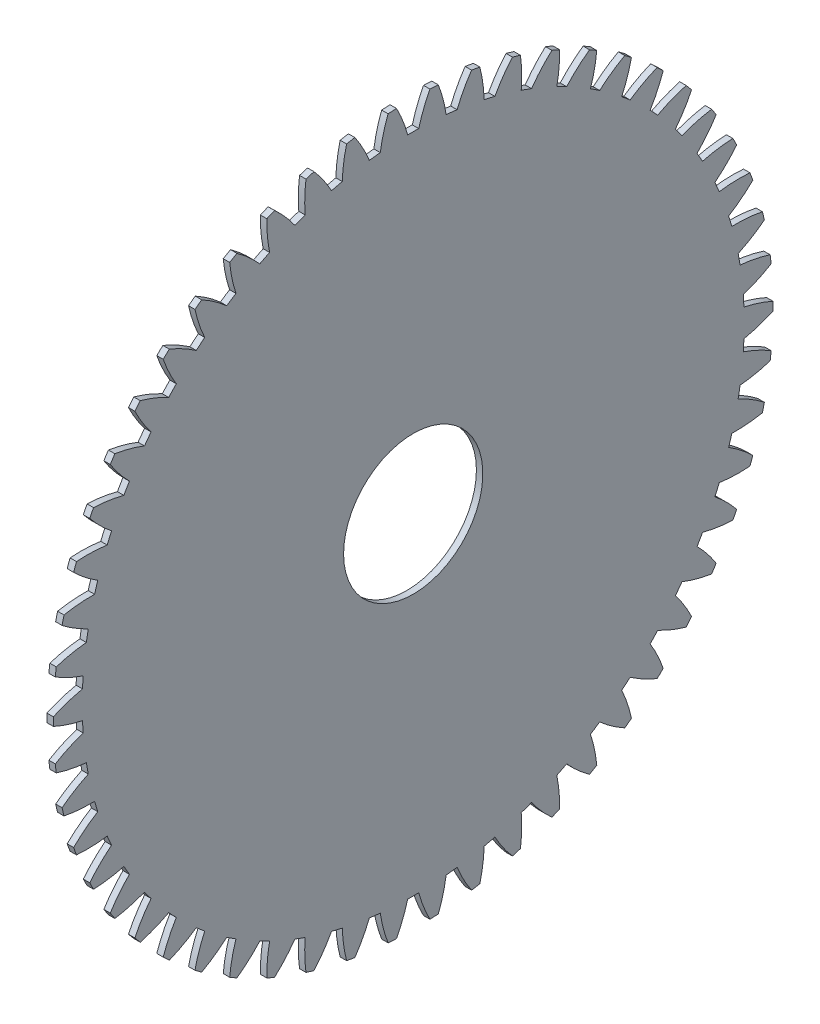
SolidWorks part; units mm, degrees
ref_plane "Plane1" through (0, 0, 0) normal (0, 0, 1) x (1, 0, 0)
ref_plane "Plane2" through (0, 0, 0) normal (0, 1, 0) x (1, 0, 0)
ref_plane "Plane3" through (0, 0, 0) normal (1, 0, 0) x (0, 0, -1)
other "Configuration Table"
sketch "HoldingSke" plane through (0, 0, 0) normal (0, 1, 0) x (1, 0, 0)
  line L0 (0, 0) -> (0.098, -0.1348)
  line L1 (-15, 0) -> (100, 0) construction
  line L2 (0, 0) -> (-2.1039, 2.3779)
  line L3 (0, 0) -> (-11.863, 4.5341)
  line L4 (0, 0) -> (5.0761, 6.9867)
  line L5 (0, 0) -> (-46.8476, -17.4728)
  line L6 (0, 0) -> (-2.4869, -1.6779)
  line L7 (-2.1039, 2.3779) -> (8.6586, 51.2059)
  line L8 (-76.2, 54.61) -> (-71.3, 54.61)
  line L9 (-71.009, 38.7566) -> (-53.1078, 45.2721)
  line L10 (-76.2, 71.12) -> (104.1128, 71.12)
  line L11 (0, 0) -> (-3, 0)
  line L12 (-76.2, 101.6) -> (-75.993, 101.6)
  line L13 (24.9733, 27.94) -> (52.9518, 28.4284)
  line L14 (24.9733, 27.94) -> (24.9743, 27.94)
  line L15 (24.9733, 27.94) -> (100.4006, 29.5858)
  line L16 (-63.627, -6) -> (-12.827, -6)
  circle A0 centre (0, 0) radius 32.5
  circle A1 centre (0, 0) radius 37.5
  circle A2 centre (0, 0) radius 37.5
  circle A3 centre (0, 0) radius 32.5
  dimension "MHD" = 75
  dimension "Hub_dia" = 75
  dimension "Bore" = 65
  dimension "MBD" = 65
  dimension "Num_teeth" = 54
  dimension "Pitch" = 0.1667
  dimension "Overall_len" = 50
  dimension "Show_teeth" = 54
  dimension "Thickness" = 3
  dimension "OAL" = 50.0001
  dimension "T_dim" = 4.9
  dimension "Ap" = 20
  dimension "H" = 19.05
  dimension "Pitch_radius" = 180.3128
  dimension "Width" = 3
  dimension "Backlash" = 0.207
  dimension "Addendum_fac" = 1
  dimension "Dedendum_fac" = 1.25
  dimension "Clearance_fac" = 0.25
  dimension "Dedendum_add" = 0.001
  dimension "Module" = 6
sketch "BasProSke" plane through (0, 0, 0) normal (0, 1, 0) x (1, 0, 0)
  line L0 (-10, 0) -> (60, 0) construction
  line L1 (0, 0) -> (0, 168)
  line L2 (0, 0) -> (3, 0)
  line L3 (3, 0) -> (3, 168)
  line L4 (3, 168) -> (0, 168)
  dimension "Thickness" = 3
  dimension "Diameter" = 336
revolve "Base-Revolve" add sketch "BasProSke" angle 360 about L0
sketch "TooCutSke" plane through (0, 0, 0) normal (1, 0, 0) x (0, 0, -1)
  line L1 (0, 0) -> (0, 107) construction
  line L2 (0, 0) -> (-5.074, 161.9205) construction
  line L3 (0, 0) -> (-18.8321, 323.3352) construction
  line L4 (-5.074, 161.9205) -> (-9.4161, 161.6676) construction
  arc A0 (2.5723, 154.4776) -> (-2.5723, 154.4776) centre (0, 0) ccw
  arc A1 (7.8281, 167.843) -> (-7.8281, 167.843) centre (0, 0) ccw
  circle A2 centre (0, 0) radius 162 construction
  circle A3 centre (0, 0) radius 152.2302 construction
  arc A4 (-2.5723, 154.4776) -> (-7.8281, 167.843) centre (-65.1337, 137.5923) ccw
  arc A5 (7.8281, 167.843) -> (2.5723, 154.4776) centre (65.1337, 137.5923) ccw
  dimension "Root_dia" = 308.998
  dimension "Overcut_dia" = 336.0508
  dimension "Pitch_dia" = 324
  dimension "Base_dia" = 304.4604
  dimension "Flank_rad" = 64.8
  dimension "Half_ang" = 3.333
  dimension "Half_CT" = 4.3495
extrude "ToothCut" cut sketch "TooCutSke" along normal through all
fillet "Breaks" [suppressed] radius 0.12
fillet "RootFillets" [suppressed] radius 1.501
pattern_circular "TeethCuts" count 54 every 6.667 about axis through (-10, 0, 0) along (1, 0, 0) of "ToothCut", "RootFillets", "Breaks"
sketch "HubNeaOneSke" plane through (0, 0, 0) normal (-1, 0, 0) x (0, 0, 1)
  circle A0 centre (0, 0) radius 37.5
  dimension "Diameter" = 75
extrude "HubNearOne" [suppressed] add sketch "HubNeaOneSke" along normal blind 47.0001
sketch "HubNeaBotSke" plane through (0, 0, 0) normal (-1, 0, 0) x (0, 0, 1)
  circle A0 centre (0, 0) radius 37.5
  dimension "Diameter" = 75
extrude "HubNearBoth" [suppressed] add sketch "HubNeaBotSke" along normal blind 23.5
ref_plane "FarPln" through (3, 0, 0) normal (1, 0, 0) x (0, 0, -1)
sketch "HubFarSke" plane through (3, 0, 0) normal (1, 0, 0) x (0, 0, -1)
  circle A0 centre (0, 0) radius 37.5
  dimension "Diameter" = 75
extrude "HubFar" [suppressed] add sketch "HubFarSke" along normal blind 23.5
sketch "BorSke" plane through (0, 0, 0) normal (1, 0, 0) x (0, 0, -1)
  circle A0 centre (0, 0) radius 32.5
  dimension "Diameter" = 65
extrude "Bore" cut sketch "BorSke" along normal mid plane 100.0001
sketch "KeySke" plane through (0, 0, 0) normal (1, 0, 0) x (0, 0, -1)
  line L0 (-10, 0) -> (-10, 37.4)
  line L1 (-10, 37.4) -> (10, 37.4)
  line L2 (10, 37.4) -> (10, 0)
  line L3 (0, 0) -> (0, 34) construction
  line L4 (-10, 0) -> (10, 0)
  dimension "Offset" = 37.4
  dimension "Width" = 20
extrude "Keyway" [suppressed] cut sketch "KeySke" along normal mid plane 100.0001
pattern_circular "Keyway2" [suppressed] count 2 every 90 about axis through (-10, 0, 0) along (1, 0, 0)
equation "' \"Module@HoldingSke\" = 6.35"
equation "' \"Num_teeth@HoldingSke\" = 12"
equation "' \"Ap@HoldingSke\" =  20"
equation "' \"Ap@HoldingSke\" = 20"
equation "' \"Width@HoldingSke\" = 0.5 * 25.4"
equation "' \"Hub_dia@HoldingSke\"= 1 * 25.4"
equation "' \"Hub_dia@HoldingSke\" = 1 * 25.4"
equation "' \"Overall_len@HoldingSke\" = 1.0 * 25.4"
equation "' \"Bore@HoldingSke\" = 0.75 * 25.4"
equation "' \"T_dim@HoldingSke\" = 0.1 * 25.4"
equation "' \"Width@KeySke\" = 0.25 * 25.4"
equation "' \"Show_teeth@HoldingSke\" = 13"
equation "' \"Backlash@HoldingSke\" = 0.009 * 25.4"
equation "' \"Addendum_fac@HoldingSke\" = 1.0"
equation "' \"Dedendum_fac@HoldingSke\" = 1.25"
equation "' \"Dedendum_add@HoldingSke\" = 0.00005 * 25.4"
equation "' \"Clearance_fac@HoldingSke\" = 0.25"
equation "\"Pitch@HoldingSke\" = 1 / \"Module@HoldingSke\""
equation "\"Overcut_dia@TooCutSke\" = (\"Num_teeth@HoldingSke\" + 2 * \"Addendum_fac@HoldingSke\") / \"Pitch@HoldingSke\" + 0.002 * 25.4"
equation "\"Pitch_dia@TooCutSke\" = \"Num_teeth@HoldingSke\" / \"Pitch@HoldingSke\""
equation "\"Base_dia@TooCutSke\" = \"Num_teeth@HoldingSke\" / \"Pitch@HoldingSke\" * cos((\"Ap@HoldingSke\"  * 3.14159265 / 180))"
equation "\"Root_dia@TooCutSke\" = (\"Num_teeth@HoldingSke\" + 2) / \"Pitch@HoldingSke\" - 2 * (\"Addendum_fac@HoldingSke\" + \"Dedendum_fac@HoldingSke\") / \"Pitch@HoldingSke\" - \"Dedendum_add@HoldingSke\" * 2"
equation "\"Half_ang@TooCutSke\" = 180 / \"Num_teeth@HoldingSke\""
equation "\"Half_CT@TooCutSke\" = \"Num_teeth@HoldingSke\" / \"Pitch@HoldingSke\" * sin((3.14159265 / 2 / \"Num_teeth@HoldingSke\")) / 2 - 7 * \"Backlash@HoldingSke\" / 4"
equation "\"Flank_rad@TooCutSke\" = \"Num_teeth@HoldingSke\" / \"Pitch@HoldingSke\" / 5"
equation "\"Radius@RootFillets\" = \"Clearance_fac@HoldingSke\" / \"Pitch@HoldingSke\" + \"Dedendum_add@HoldingSke\""
equation "\"Break_rad@Breaks\" = 0.02 / \"Pitch@HoldingSke\""
equation "\"Thickness@HoldingSke\" = \"Width@HoldingSke\""
equation "\"OAL@HoldingSke\" = \"Thickness@HoldingSke\""
equation "\"MHD@HoldingSke\" = (\"Num_teeth@HoldingSke\" + 2) / \"Pitch@HoldingSke\" - 2 * (\"Addendum_fac@HoldingSke\" + \"Dedendum_fac@HoldingSke\")  / \"Pitch@HoldingSke\" - \"Dedendum_add@HoldingSke\" * 2"
equation "\"MBD@HoldingSke\" = (\"Num_teeth@HoldingSke\" + 2) / \"Pitch@HoldingSke\" - 2 * (\"Addendum_fac@HoldingSke\" + \"Dedendum_fac@HoldingSke\")  / \"Pitch@HoldingSke\" - \"Dedendum_add@HoldingSke\" * 2 - 0.002 * 25.4"
equation "\"MHD@HoldingSke\" = ((sgn( \"MHD@HoldingSke\" - \"Hub_dia@HoldingSke\" )-1)*( \"MHD@HoldingSke\" - \"Hub_dia@HoldingSke\" ))/-2+ \"Hub_dia@HoldingSke\""
equation "\"MBD@HoldingSke\" = ((sgn( \"MBD@HoldingSke\" - \"Bore@HoldingSke\" )-1)*( \"MBD@HoldingSke\" - \"Bore@HoldingSke\" ))/-2+ \"Bore@HoldingSke\""
equation "\"OAL@HoldingSke\" = ((sgn( \"OAL@HoldingSke\" - \"Overall_len@HoldingSke\" )+1)*( \"OAL@HoldingSke\" - \"Overall_len@HoldingSke\" ))/2 + \"Overall_len@HoldingSke\" + 0.000002 * 25.4"
equation "\"Num_teeth@TeethCuts\" = int( \"Show_teeth@HoldingSke\" ) + 1"
equation "\"Num_teeth@TeethCuts\" = ((sgn( \"Num_teeth@TeethCuts\" - \"Num_teeth@HoldingSke\" )-1)*( \"Num_teeth@TeethCuts\" - \"Num_teeth@HoldingSke\" ))/-2+ \"Num_teeth@HoldingSke\""
equation "\"Num_teeth@TeethCuts\" = ((sgn( \"Num_teeth@TeethCuts\" - 2.0)+1)*( \"Num_teeth@TeethCuts\" - 2.0))/2 +2.0"
equation "\"Angle@TeethCuts\" = 360.0 / \"Num_teeth@HoldingSke\""
equation "\"Diameter@BasProSke\" = (\"Num_teeth@HoldingSke\" + 2 * \"Addendum_fac@HoldingSke\") / \"Pitch@HoldingSke\""
equation "\"Thickness@BasProSke\"  = \"Thickness@HoldingSke\""
equation "' \"Fillet_rad@BasProSke\" =  \"Thickness@HoldingSke\" * 0.05"
equation "' \"Fillet_rad@BasProSke\" = \"Thickness@HoldingSke\" * 0.05"
equation "\"MHD@HoldingSke\" = ((sgn( \"MHD@HoldingSke\" - \"Root_dia@TooCutSke\" )-1)*( \"MHD@HoldingSke\" - \"Root_dia@TooCutSke\" ))/-2+ \"Root_dia@TooCutSke\""
equation "\"Diameter@HubNeaOneSke\" = \"MHD@HoldingSke\""
equation "\"Length@HubNearOne\" = \"OAL@HoldingSke\" - \"Thickness@BasProSke\""
equation "\"Diameter@HubNeaBotSke\" = \"MHD@HoldingSke\""
equation "\"Length@HubNearBoth\" = ( \"OAL@HoldingSke\" - \"Thickness@BasProSke\" ) / 2.0"
equation "\"Thickness@FarPln\" = \"Thickness@BasProSke\""
equation "\"Diameter@HubFarSke\" = \"MHD@HoldingSke\""
equation "\"Length@HubFar\" = ( \"OAL@HoldingSke\" - \"Thickness@BasProSke\" ) / 2.0"
equation "\"Diameter@BorSke\" = \"MBD@HoldingSke\""
equation "\"D1@Bore\" = \"OAL@HoldingSke\" * 2.0"
equation "\"D1@Keyway\" = \"OAL@HoldingSke\" * 2.0"
equation "\"Offset@KeySke\" = \"T_dim@HoldingSke\" + \"MBD@HoldingSke\" / 2.0"
